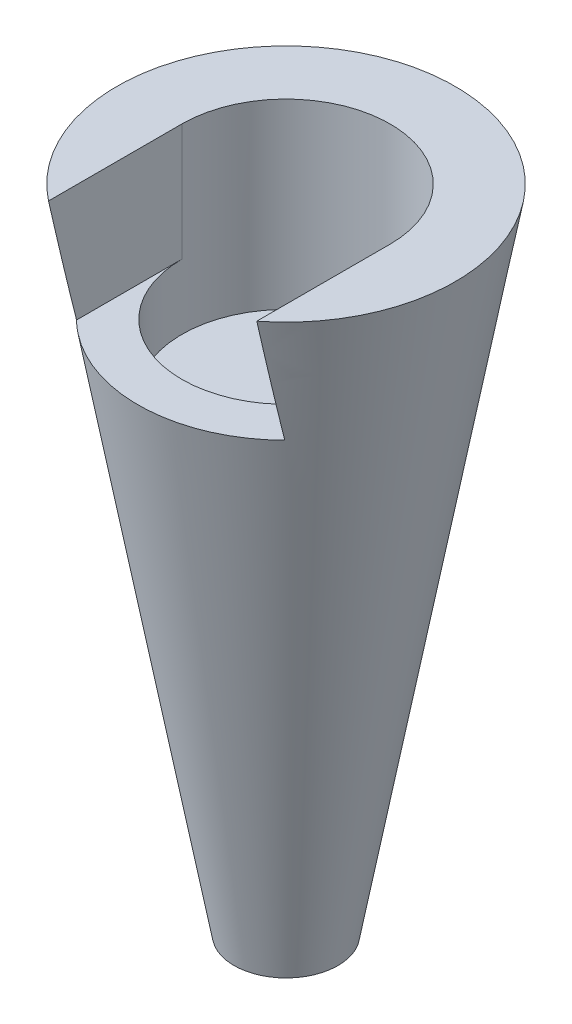
SolidWorks part; units mm, degrees
ref_plane "Front Plane" through (0, 0, 0) normal (0, 0, 1) x (1, 0, 0)
ref_plane "Top Plane" through (0, 0, 0) normal (0, 1, 0) x (1, 0, 0)
ref_plane "Right Plane" through (0, 0, 0) normal (1, 0, 0) x (0, 0, -1)
sketch "Sketch1" plane through (0, 0, 0) normal (0, 0, 1) x (1, 0, 0)
  line L0 (0, 0) -> (0, 50) construction
  line L1 (0, 50) -> (-13, 50)
  line L2 (-13, 50) -> (-4, 0)
  line L3 (-4, 0) -> (0, 0)
  line L4 (0, 0) -> (0, 50)
  dimension "D1" = 50
  dimension "D2" = 13
  dimension "D3" = 4
revolve "Revolve1" add sketch "Sketch1" angle 360 about L0
sketch "Sketch2" plane through (0, 0, 0) normal (0, -1, 0) x (1, 0, 0)
  line L1 (-2.25, -1.5) -> (2.25, -1.5)
  line L2 (-2.25, -1.5) -> (-2.25, 1.5)
  line L3 (-2.25, 1.5) -> (2.25, 1.5)
  line L4 (2.25, -1.5) -> (2.25, 1.5)
  line L5 (-2.25, -1.5) -> (2.25, 1.5) construction
  line L6 (-2.25, 1.5) -> (2.25, -1.5) construction
  point P0 (0, 0)
  dimension "D1" = 3
  dimension "D2" = 4.5
extrude "Cut-Extrude1" cut sketch "Sketch2" against normal blind 6
sketch "Sketch3" plane through (0, 0, -1.5) normal (0, 0, 1) x (1, 0, 0)
  line L0 (-2.25, 0) -> (2.25, 0) construction
  circle A0 centre (0, 3.5) radius 1.15
  dimension "D1" = 2.3
  dimension "D2" = 3.5
extrude "Cut-Extrude2" cut sketch "Sketch3" against normal blind 6
sketch "Sketch4" plane through (0, 50, 0) normal (0, 1, 0) x (1, 0, 0)
  line L0 (-8, 0) -> (-8, -14.0026)
  line L1 (-8, -14.0026) -> (8, -14.0026)
  line L2 (8, -14.0026) -> (8, 0)
  arc A0 (8, 0) -> (-8, 0) centre (0, 0) ccw
  dimension "D1" = 16
extrude "Cut-Extrude3" cut sketch "Sketch4" against normal blind 9
sketch "Sketch5" plane through (0, 41, 0) normal (0, 1, 0) x (1, 0, 0)
  circle A0 centre (0, 0) radius 8
extrude "Cut-Extrude4" cut sketch "Sketch5" against normal blind 5
